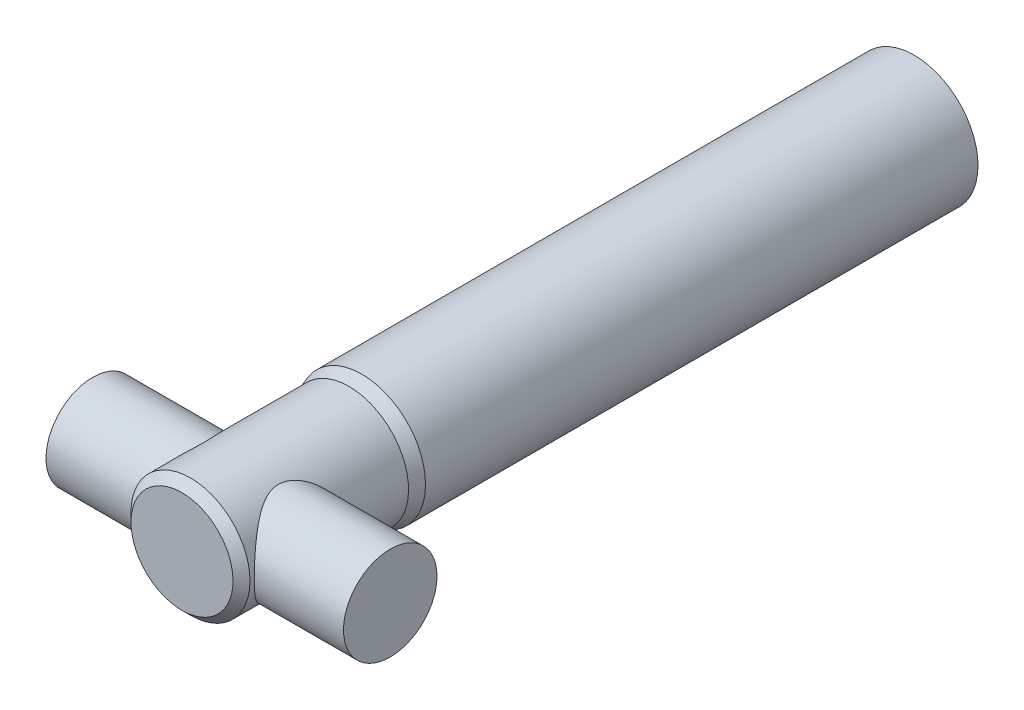
SolidWorks part; units mm, degrees
ref_plane "Front Plane" through (0, 0, 0) normal (0, 0, 1) x (1, 0, 0)
ref_plane "Top Plane" through (0, 0, 0) normal (0, 1, 0) x (1, 0, 0)
ref_plane "Right Plane" through (0, 0, 0) normal (1, 0, 0) x (0, 0, -1)
sketch "Sketch2" plane through (0, 0, 0) normal (0, 0, 1) x (1, 0, 0)
  circle A0 centre (0, 0) radius 15
  dimension "D1" = 30
extrude "Boss-Extrude2" add sketch "Sketch2" along normal blind 130
sketch "Sketch4" plane through (0, 0, 0) normal (1, 0, 0) x (0, 0, -1)
  line L0 (-130, 0) -> (-172.3, 0)
  line L1 (-130, 15) -> (-130, -15) construction
  line L2 (-172.3, 0) -> (-172.3, 14)
  line L3 (-172.3, 14) -> (-133, 14)
  line L4 (-133, 14) -> (-130, 15)
  line L5 (-130, 15) -> (-130, 0)
  dimension "D1" = 3
  dimension "D2" = 14
  dimension "D3" = 42.3
revolve "Revolve1" add sketch "Sketch4" angle 360 about L0
sketch "Sketch5" plane through (0, 0, 0) normal (1, 0, 0) x (0, 0, -1)
  line L0 (-172.3, 14) -> (-172.3, -14) construction
  circle A0 centre (-158.3, 0) radius 11
  dimension "D1" = 22
  dimension "D2" = 14
extrude "Boss-Extrude3" add sketch "Sketch5" along normal mid plane 70
chamfer "Chamfer1" distance 2 angle 45 1 edges at (0, 14, 172.3)
